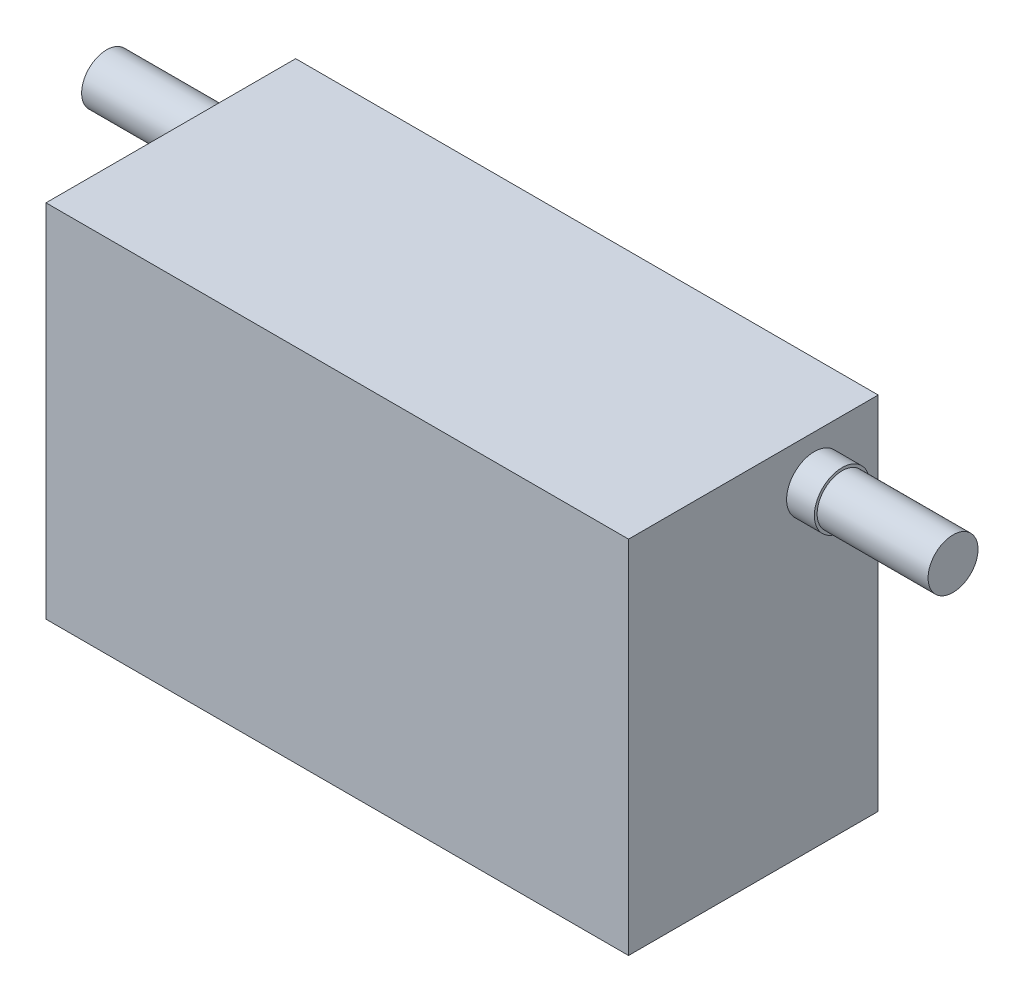
SolidWorks part; units mm, degrees
ref_plane "Front Plane" through (0, 0, 0) normal (0, 0, 1) x (1, 0, 0)
ref_plane "Top Plane" through (0, 0, 0) normal (0, 1, 0) x (1, 0, 0)
ref_plane "Right Plane" through (0, 0, 0) normal (1, 0, 0) x (0, 0, -1)
sketch "Sketch1" plane through (0, 0, 0) normal (0, 0, 1) x (1, 0, 0)
  line L1 (52.5, -32.5) -> (-52.5, -32.5)
  line L2 (52.5, -32.5) -> (52.5, 32.5)
  line L3 (52.5, 32.5) -> (-52.5, 32.5)
  line L4 (-52.5, -32.5) -> (-52.5, 32.5)
  line L5 (52.5, -32.5) -> (-52.5, 32.5) construction
  line L6 (52.5, 32.5) -> (-52.5, -32.5) construction
  point P0 (0, 0)
  dimension "D1" = 105
  dimension "D2" = 65
extrude "Boss-Extrude1" add sketch "Sketch1" along normal blind 45
sketch "Sketch2" plane through (-52.5, 0, 0) normal (-1, 0, 0) x (0, 0, 1)
  circle A0 centre (9.0805, 21.4211) radius 5
  dimension "D1" = 10
extrude "Boss-Extrude2" add sketch "Sketch2" along normal blind 5
sketch "Sketch3" plane through (-57.5, 0, 0) normal (-1, 0, 0) x (0, 0, 1)
  circle A0 centre (9.0805, 21.4211) radius 4.5
  dimension "D1" = 9
extrude "Boss-Extrude3" add sketch "Sketch3" along normal blind 20
sketch "Sketch4" plane through (52.5, 0, 0) normal (1, 0, 0) x (0, 0, -1)
  circle A0 centre (-11.5131, 24.4236) radius 5
  dimension "D1" = 10
extrude "Boss-Extrude4" add sketch "Sketch4" along normal blind 5
sketch "Sketch5" plane through (57.5, 0, 0) normal (1, 0, 0) x (0, 0, -1)
  circle A0 centre (-11.5131, 24.4236) radius 4.5
  dimension "D1" = 9
extrude "Boss-Extrude5" add sketch "Sketch5" along normal blind 20
